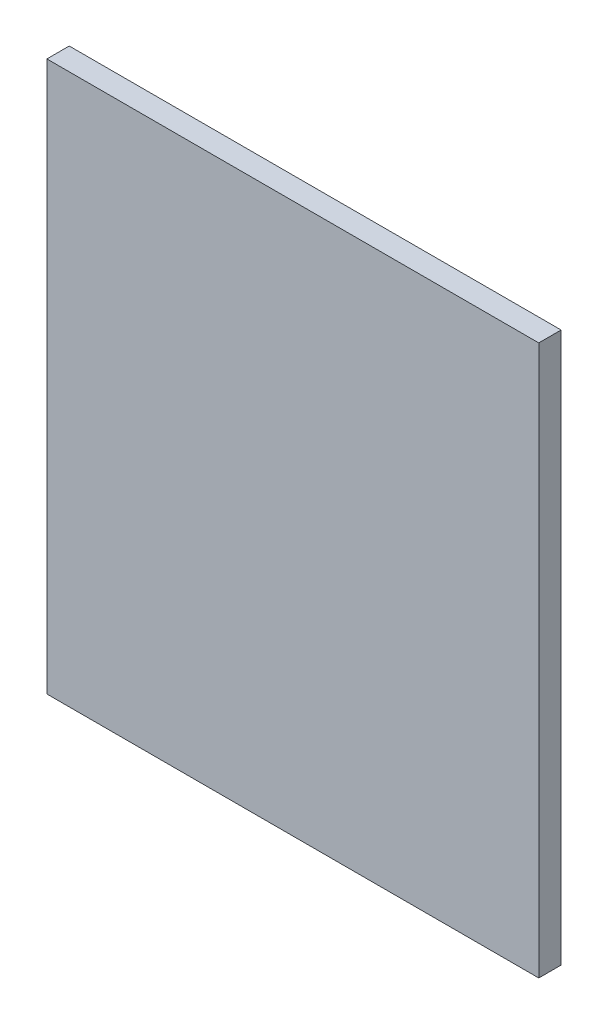
SolidWorks part; units mm, degrees
ref_plane "Front Plane" through (0, 0, 0) normal (0, 0, 1) x (1, 0, 0)
ref_plane "Top Plane" through (0, 0, 0) normal (0, 1, 0) x (1, 0, 0)
ref_plane "Right Plane" through (0, 0, 0) normal (1, 0, 0) x (0, 0, -1)
sketch "Sketch1" plane through (0, 0, 0) normal (0, 0, 1) x (1, 0, 0)
  line L1 (0, 0) -> (139.7, 0)
  line L2 (0, 0) -> (0, 156.21)
  line L3 (0, 156.21) -> (139.7, 156.21)
  line L4 (139.7, 0) -> (139.7, 156.21)
  dimension "D1" = 156.21
  dimension "D2" = 139.7
extrude "Boss-Extrude1" add sketch "Sketch1" along normal blind 6.35
